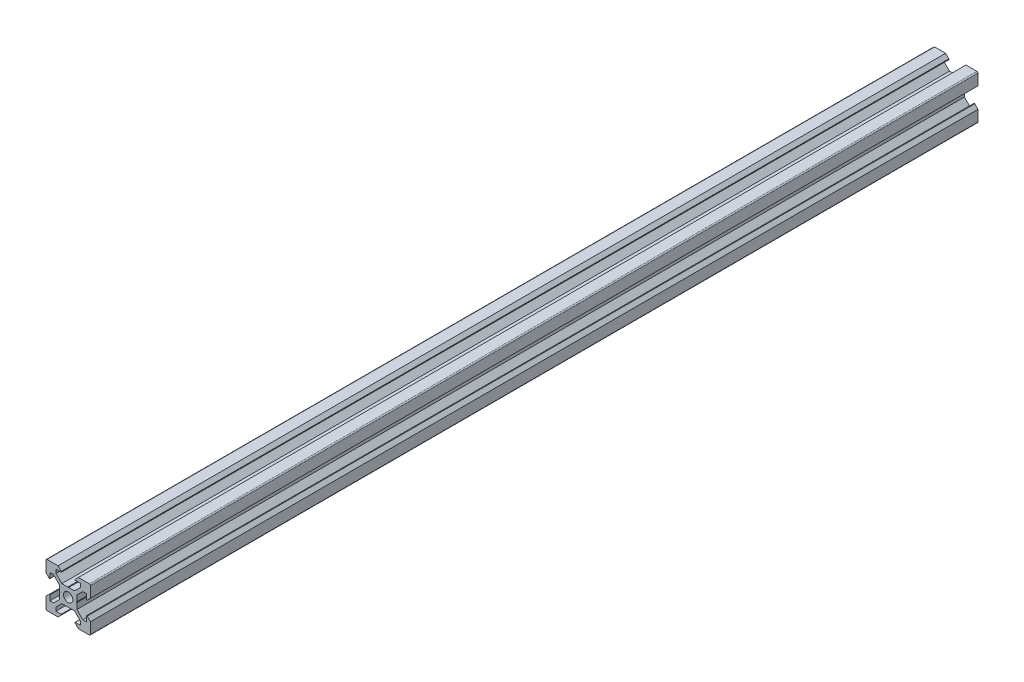
SolidWorks part; units mm, degrees
material "6061-T6 (SS)"
ref_plane "Front Plane" through (0, 0, 0) normal (0, 0, 1) x (1, 0, 0)
ref_plane "Top Plane" through (0, 0, 0) normal (0, 1, 0) x (1, 0, 0)
ref_plane "Right Plane" through (0, 0, 0) normal (1, 0, 0) x (0, 0, -1)
sketch "Sketch1" plane through (0, 0, 0) normal (0, 0, 1) x (1, 0, 0)
  line L1 (9.5, -10) -> (-9.5, -10)
  line L2 (10, -9.5) -> (10, 9.5)
  line L3 (9.5, 10) -> (-9.5, 10)
  line L4 (-10, -9.5) -> (-10, 9.5)
  line L5 (10, -10) -> (-10, 10) construction
  line L6 (10, 10) -> (-10, -10) construction
  circle A0 centre (0, 0) radius 2.1
  arc A1 (-9.5, 10) -> (-10, 9.5) centre (-9.5, 9.5) ccw
  arc A2 (10, 9.5) -> (9.5, 10) centre (9.5, 9.5) ccw
  arc A3 (9.5, -10) -> (10, -9.5) centre (9.5, -9.5) ccw
  arc A4 (-9.5, -10) -> (-10, -9.5) centre (-9.5, -9.5) cw
  point P0 (0, 0)
  line B0 (0, 0) -> (0, 10) construction
  line B1 (0, 3.69) -> (-0.21, 3.9)
  line B2 (-0.21, 3.9) -> (-2.8393, 3.9)
  line B3 (-2.8393, 3.9) -> (-5.5, 6.5607)
  line B4 (-5.5, 6.5607) -> (-5.5, 8.2)
  line B5 (-5.5, 8.2) -> (-3.125, 8.2)
  line B6 (-3.125, 8.2) -> (-3.125, 8.545)
  line B7 (-3.125, 8.545) -> (-4.58, 10)
  line B8 (-4.58, 10) -> (4.58, 10)
  line B9 (0, 0) -> (-5.9132, 5.9132) construction
  line B10 (3.125, 8.545) -> (4.58, 10)
  line B11 (3.125, 8.2) -> (3.125, 8.545)
  line B12 (5.5, 8.2) -> (3.125, 8.2)
  line B13 (5.5, 6.5607) -> (5.5, 8.2)
  line B14 (2.8393, 3.9) -> (5.5, 6.5607)
  line B15 (0.21, 3.9) -> (2.8393, 3.9)
  line B16 (0, 3.69) -> (0.21, 3.9)
  line B17 (0, 0) -> (-10, 0) construction
  line B18 (-3.69, 0) -> (-3.9, -0.21)
  line B19 (-3.9, -0.21) -> (-3.9, -2.8393)
  line B20 (-3.9, -2.8393) -> (-6.5607, -5.5)
  line B21 (-6.5607, -5.5) -> (-8.2, -5.5)
  line B22 (-8.2, -5.5) -> (-8.2, -3.125)
  line B23 (-8.2, -3.125) -> (-8.545, -3.125)
  line B24 (-8.545, -3.125) -> (-10, -4.58)
  line B25 (-10, -4.58) -> (-10, 4.58)
  line B26 (0, 0) -> (-5.9132, -5.9132) construction
  line B27 (-8.545, 3.125) -> (-10, 4.58)
  line B28 (-8.2, 3.125) -> (-8.545, 3.125)
  line B29 (-8.2, 5.5) -> (-8.2, 3.125)
  line B30 (-6.5607, 5.5) -> (-8.2, 5.5)
  line B31 (-3.9, 2.8393) -> (-6.5607, 5.5)
  line B32 (-3.9, 0.21) -> (-3.9, 2.8393)
  line B33 (-3.69, 0) -> (-3.9, 0.21)
  line B34 (0, 0) -> (0, -10) construction
  line B35 (0, -3.69) -> (0.21, -3.9)
  line B36 (0.21, -3.9) -> (2.8393, -3.9)
  line B37 (2.8393, -3.9) -> (5.5, -6.5607)
  line B38 (5.5, -6.5607) -> (5.5, -8.2)
  line B39 (5.5, -8.2) -> (3.125, -8.2)
  line B40 (3.125, -8.2) -> (3.125, -8.545)
  line B41 (3.125, -8.545) -> (4.58, -10)
  line B42 (4.58, -10) -> (-4.58, -10)
  line B43 (0, 0) -> (5.9132, -5.9132) construction
  line B44 (-3.125, -8.545) -> (-4.58, -10)
  line B45 (-3.125, -8.2) -> (-3.125, -8.545)
  line B46 (-5.5, -8.2) -> (-3.125, -8.2)
  line B47 (-5.5, -6.5607) -> (-5.5, -8.2)
  line B48 (-2.8393, -3.9) -> (-5.5, -6.5607)
  line B49 (-0.21, -3.9) -> (-2.8393, -3.9)
  line B50 (0, -3.69) -> (-0.21, -3.9)
  line B51 (0, 0) -> (10, 0) construction
  line B52 (3.69, 0) -> (3.9, 0.21)
  line B53 (3.9, 0.21) -> (3.9, 2.8393)
  line B54 (3.9, 2.8393) -> (6.5607, 5.5)
  line B55 (6.5607, 5.5) -> (8.2, 5.5)
  line B56 (8.2, 5.5) -> (8.2, 3.125)
  line B57 (8.2, 3.125) -> (8.545, 3.125)
  line B58 (8.545, 3.125) -> (10, 4.58)
  line B59 (10, 4.58) -> (10, -4.58)
  line B60 (0, 0) -> (5.9132, 5.9132) construction
  line B61 (8.545, -3.125) -> (10, -4.58)
  line B62 (8.2, -3.125) -> (8.545, -3.125)
  line B63 (8.2, -5.5) -> (8.2, -3.125)
  line B64 (6.5607, -5.5) -> (8.2, -5.5)
  line B65 (3.9, -2.8393) -> (6.5607, -5.5)
  line B66 (3.9, -0.21) -> (3.9, -2.8393)
  line B67 (3.69, 0) -> (3.9, -0.21)
  dimension "D1" = 4.2
  dimension "D3" = 0.5
  dimension "D2" = 20
sketch_block_instance "V Slot 1-4"
sketch_block "V Slot 1" parameters "D1"=10, "D2"=11, "D3"=4.3, "D4"=1.8, "D5"=0.21, "D6"=45, "D7"=9.16, "D8"=1.5, "D9"=6.25
sketch_block_instance "V Slot 1-5"
sketch_block_instance "V Slot 1-6"
sketch_block_instance "V Slot 1-7"
extrude "Boss-Extrude1" add sketch "Sketch1" along normal blind 400 contours B67 B52 B53 B54 B55 B56 B57 B58 L2 A2 L3 B10 B11 B12 B13 B14 B15 B16 B1 B2 B3 B4 B5 B6 B7 A1 L4 B27 B28 B29 B30 B31 B32 B33 B18 B19 B20 B21 B22 B23 B24 A4 L1 B44 B45 B46 B47 B48 B49
